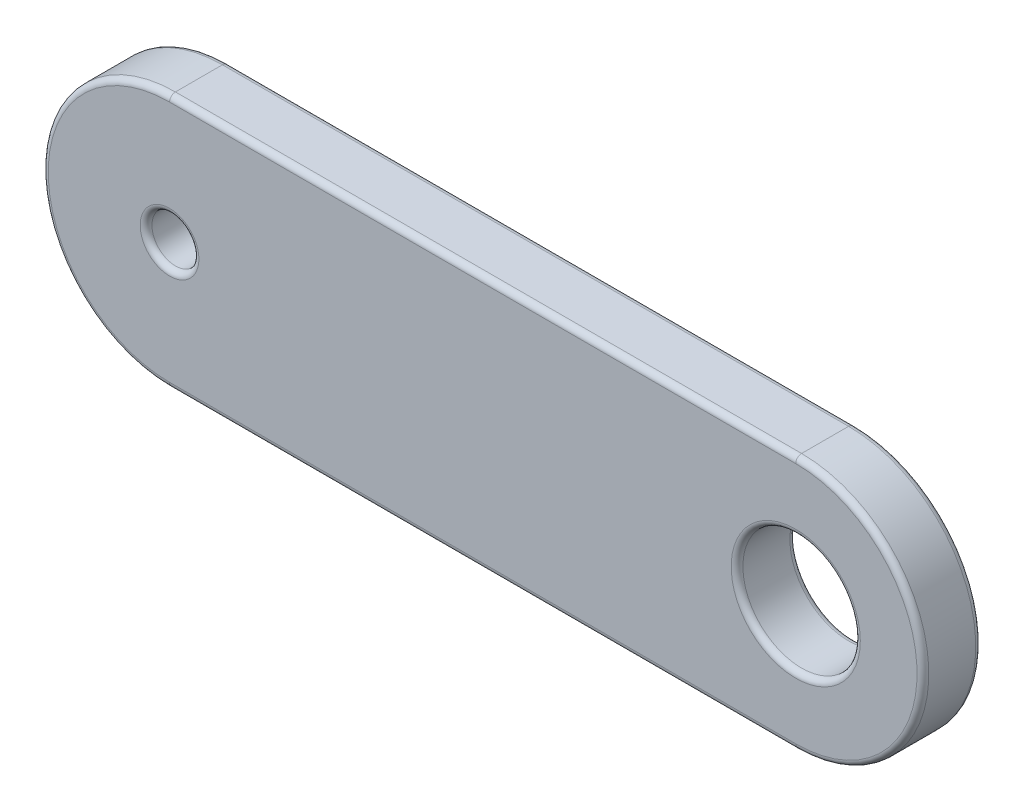
SolidWorks part; units mm, degrees
ref_plane "Płaszczyzna przednia" through (0, 0, 0) normal (0, 0, 1) x (1, 0, 0)
ref_plane "Płaszczyzna górna" through (0, 0, 0) normal (0, 1, 0) x (1, 0, 0)
ref_plane "Płaszczyzna prawa" through (0, 0, 0) normal (1, 0, 0) x (0, 0, -1)
sketch "Szkic1" plane through (0, 0, 0) normal (0, 0, 1) x (1, 0, 0)
  line L0 (-8, 0) -> (8, 0) construction
  line L1 (-8, 3.25) -> (8, 3.25)
  line L2 (-8, -3.25) -> (8, -3.25)
  arc A0 (-8, 3.25) -> (-8, -3.25) centre (-8, 0) ccw
  arc A1 (8, -3.25) -> (8, 3.25) centre (8, 0) ccw
  circle A2 centre (-8, 0) radius 0.6
  circle A3 centre (8, 0) radius 1.5
  point P2 (0, 0)
  dimension "D3" = 3
  dimension "D4" = 1.2
  dimension "D1" = 16
  dimension "D2" = 6.5
extrude "Dodanie-wyciągnięcie1" add sketch "Szkic1" along normal mid plane 1.5
fillet "Zaokrąglenie1" radius 0.15 12 edges at (9.5, 0, -0.75) (-7.4, 0, -0.75) (0, -3.25, -0.75) (11.25, 0, -0.75) (0, 3.25, -0.75) (-11.25, 0, -0.75) (9.5, 0, 0.75) (0, 3.25, 0.75) (11.25, 0, 0.75) (0, -3.25, 0.75) (-11.25, 0, 0.75) (-7.4, 0, 0.75)
